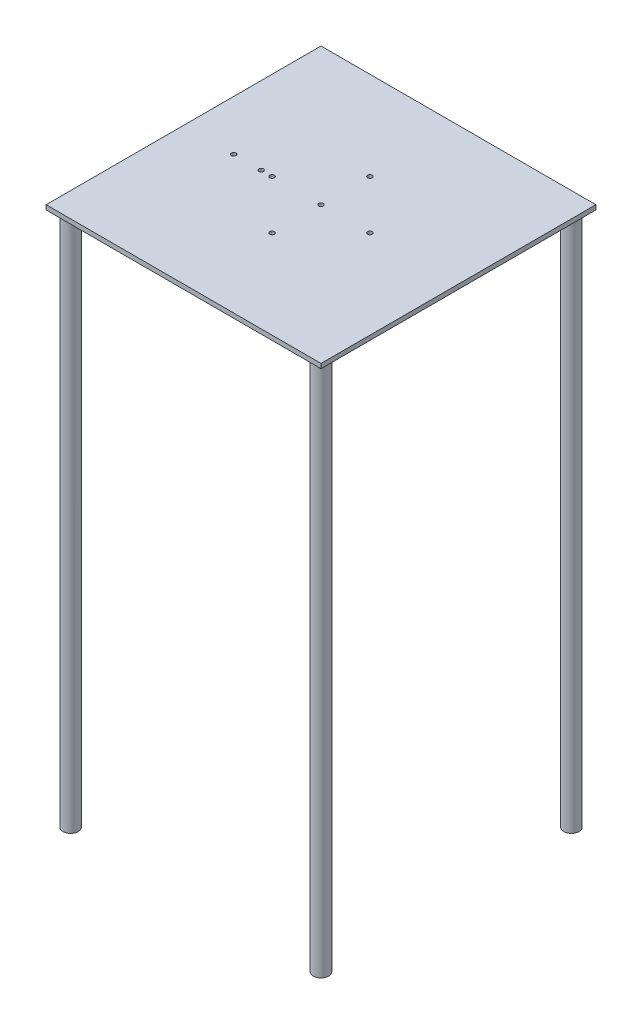
SolidWorks part; units mm, degrees
ref_plane "Front Plane" through (0, 0, 0) normal (0, 0, 1) x (1, 0, 0)
ref_plane "Top Plane" through (0, 0, 0) normal (0, 1, 0) x (1, 0, 0)
ref_plane "Right Plane" through (0, 0, 0) normal (1, 0, 0) x (0, 0, -1)
sketch "Sketch1" plane through (0, 0, 0) normal (0, 1, 0) x (1, 0, 0)
  line L0 (-180, 90) -> (0, 90) construction
  line L1 (0, 0) -> (-180, 0)
  line L2 (0, 0) -> (0, 180)
  line L3 (0, 180) -> (-180, 180)
  line L4 (-180, 0) -> (-180, 180)
  line L5 (-90, 180) -> (-90, 0) construction
  circle A2 centre (-90, 90) radius 1.5
  circle A3 centre (-58, 90) radius 1.5
  circle A4 centre (-122, 90) radius 1.5
  circle A5 centre (-90, 122) radius 1.5
  circle A6 centre (-90, 58) radius 1.5
  point P9 (0, 0)
  dimension "D5" = 3
  dimension "D6" = 3
  dimension "D9" = 3
  dimension "D1" = 180
  dimension "D2" = 180
  dimension "D7" = 32
  dimension "D10" = 32
extrude "Boss-Extrude1" add sketch "Sketch1" along normal blind 3
sketch "Sketch2" plane through (0, 3, 0) normal (0, 1, 0) x (1, 0, 0)
  line L0 (-138.1827, 180) -> (-138.1827, 0) construction
  line L1 (0, 180) -> (-180, 180) construction
  line L2 (-180, 0) -> (0, 0) construction
  line L3 (-90, 180) -> (-90, 0) construction
  line L4 (-147.1827, 180) -> (-147.1827, 0) construction
  line L5 (-129.1827, 180) -> (-129.1827, 0) construction
  circle A0 centre (-147.1827, 90) radius 1.5
  circle A1 centre (-129.1827, 90) radius 1.5
  point P10 (-138.1827, 90)
  dimension "D3" = 3
  dimension "D1" = 48.1827
  dimension "D2" = 9
extrude "Cut-Extrude1" cut sketch "Sketch2" against normal through all
sketch "Sketch3" plane through (0, 0, 0) normal (0, -1, 0) x (1, 0, 0)
  line L0 (0, 0) -> (-180, 0) construction
  line L1 (-180, 0) -> (-180, -180) construction
  line L2 (-90, 0) -> (-90, -180) construction
  line L3 (-180, -90) -> (0, -90) construction
  circle A0 centre (-172, -8) radius 5
  circle A1 centre (-8, -8) radius 5
  circle A2 centre (-8, -172) radius 5
  circle A3 centre (-172, -172) radius 5
  dimension "D1" = 10
  dimension "D2" = 8
  dimension "D3" = 8
extrude "Boss-Extrude2" add sketch "Sketch3" along normal blind 350
